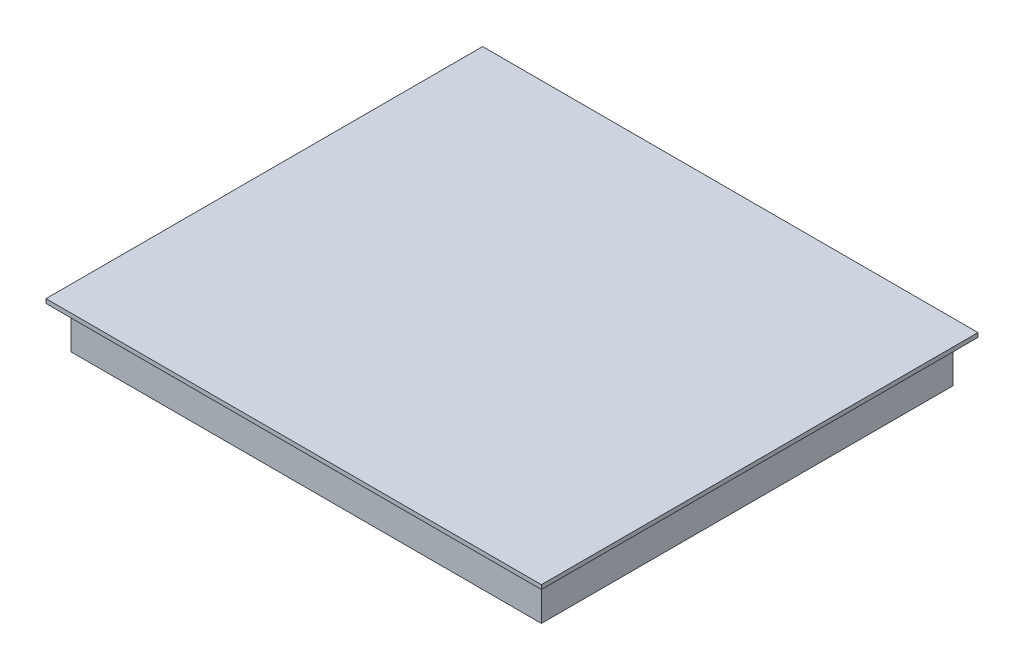
SolidWorks part; units mm, degrees
ref_plane "Спереди" through (0, 0, 0) normal (0, 0, 1) x (1, 0, 0)
ref_plane "Сверху" through (0, 0, 0) normal (0, 1, 0) x (1, 0, 0)
ref_plane "Справа" through (0, 0, 0) normal (1, 0, 0) x (0, 0, -1)
sketch "Эскиз1" plane through (0, 0, 0) normal (0, 1, 0) x (1, 0, 0)
  line L1 (-280, 245) -> (280, 245)
  line L2 (-280, 245) -> (-280, -245)
  line L3 (-280, -245) -> (280, -245)
  line L4 (280, 245) -> (280, -245)
  line L5 (-280, 245) -> (280, -245) construction
  line L6 (-280, -245) -> (280, 245) construction
  point P0 (0, 0)
extrude "Бобышка-Вытянуть1" add sketch "Эскиз1" along normal blind 50
sketch "Эскиз2" plane through (0, 50, 0) normal (0, 1, 0) x (1, 0, 0)
  line L1 (-295, 260) -> (295, 260)
  line L2 (-295, 260) -> (-295, -260)
  line L3 (-295, -260) -> (295, -260)
  line L4 (295, 260) -> (295, -260)
  line L5 (-295, 260) -> (295, -260) construction
  line L6 (-295, -260) -> (295, 260) construction
  point P0 (0, 0)
extrude "Бобышка-Вытянуть2" add sketch "Эскиз2" along normal blind 5
